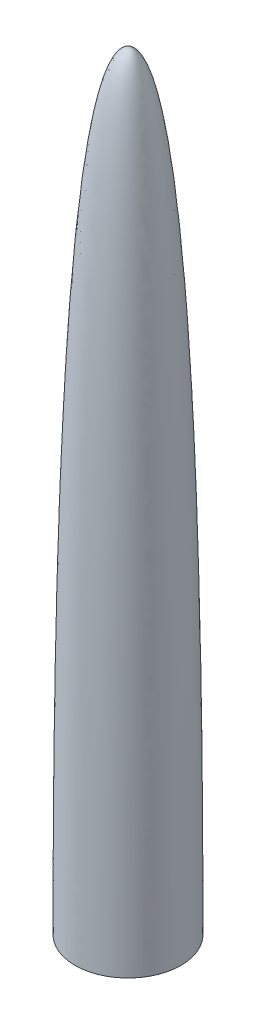
SolidWorks part; units mm, degrees
ref_plane "Front Plane" through (0, 0, 0) normal (0, 0, 1) x (1, 0, 0)
ref_plane "Top Plane" through (0, 0, 0) normal (0, 1, 0) x (1, 0, 0)
ref_plane "Right Plane" through (0, 0, 0) normal (1, 0, 0) x (0, 0, -1)
sketch "Sketch1" plane through (0, 0, 0) normal (0, 0, 1) x (1, 0, 0)
  line L2 (0, 409.6542) -> (0, 412.75)
  line L3 (0, 412.75) -> (25.4, 412.75) construction
  line L4 (25.4, 412.75) -> (28.4988, 152.4) construction
  line L5 (28.4988, 152.4) -> (28.4988, 0) construction
  line L6 (26.492, 0) -> (28.4988, 0)
  line L9 (2.0066, 409.6542) -> (0, 409.6542)
  line L10 (0, 0) -> (0, 412.75) construction
  line L11 (2.0066, 2.0066) -> (2.0066, 409.6542) construction
  line L14 (26.492, 2.0066) -> (26.492, 0)
  line L15 (0, 0) -> (28.4988, 0) construction
  line L16 (2.0066, 2.0066) -> (26.492, 2.0066) construction
  spline S0 degree 3 poles (0, 412.75) (25.4, 412.75) (28.4988, 152.4) (28.4988, 0) knots 0 0 0 0 1 1 1 1
  spline S1 degree 1 poles (2.0066, 409.6542) (26.492, 2.0066) knots 0 0 1 1 construction
  spline S2 degree 3 poles (2.0066, 409.6542) (2.1497, 409.5092) (2.4115, 409.2214) (2.9875, 408.4935) (3.7207, 407.3731) (4.6173, 405.6817) (5.8072, 402.9922) (7.2649, 398.8478) (8.9345, 392.7166) (10.5156, 385.5034) (12.502, 374.5343) (14.7569, 358.4494) (17.113, 335.8365) (19.1403, 310.384) (20.8617, 282.5586) (22.3006, 252.8242) (23.4806, 221.6432) (24.4257, 189.4777) (25.1597, 156.789) (25.7067, 124.0383) (26.0265, 97.0784) (26.2128, 75.9405) (26.3208, 60.3596) (26.4, 45.1088) (26.4445, 32.7228) (26.4687, 23.037) (26.4815, 15.8904) (26.4881, 10.0422) (26.4911, 5.4243) (26.4918, 3.1486) (26.492, 2.0066) knots 0.046987 0.046987 0.046987 0.046987 0.054398 0.06181 0.076632 0.091454 0.106277 0.135922 0.165567 0.195212 0.224856 0.284146 0.343436 0.402726 0.462016 0.521305 0.580595 0.639885 0.699175 0.758465 0.817754 0.847399 0.877044 0.906689 0.936334 0.951156 0.965979 0.980801 0.988213 0.995624 0.995624 0.995624 0.995624
  dimension "D5" = 152.4
  dimension "D1" = 28.4988
  dimension "D2" = 2.0066
  dimension "D4" = 25.4
ref_axis "Central Axis" through (0, 433.3875, 0) along (0, -1, 0)
revolve "Revolve1" add sketch "Sketch1" angle 360 about axis through (0, 433.3875, 0) along (0, -1, 0)
